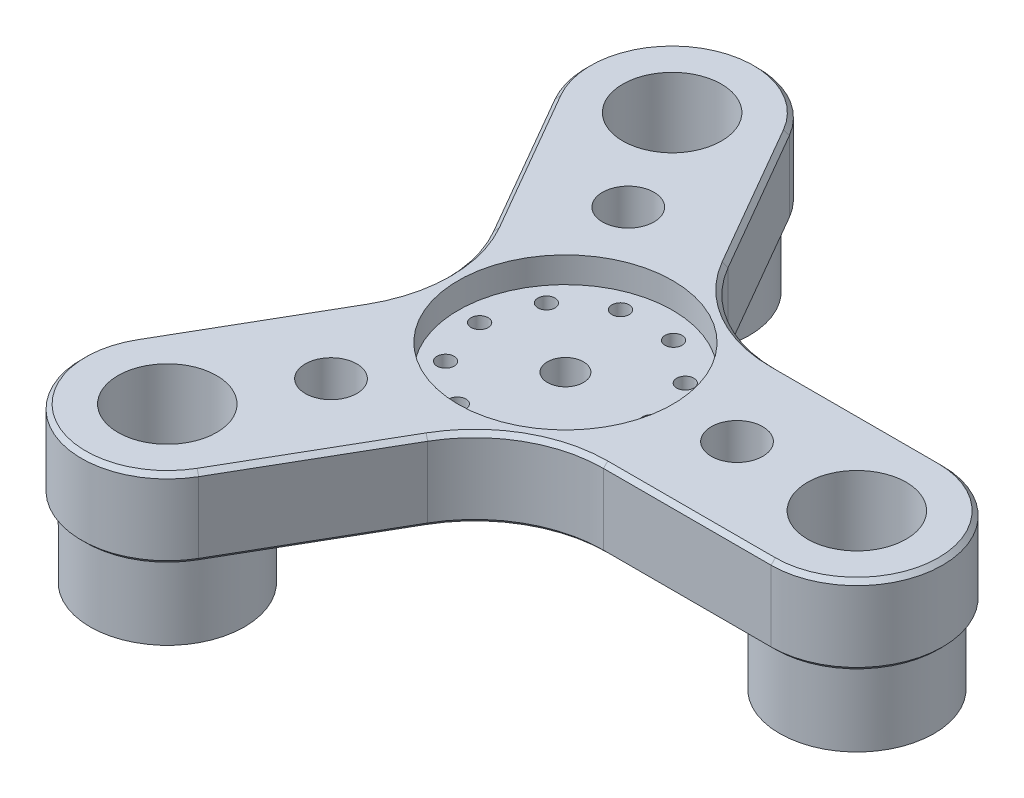
SolidWorks part; units mm, degrees
material "ﾒﾗﾐﾝ樹脂"
ref_plane "正面" through (0, 0, 0) normal (0, 0, 1) x (1, 0, 0)
ref_plane "平面" through (0, 0, 0) normal (0, 1, 0) x (1, 0, 0)
ref_plane "右側面" through (0, 0, 0) normal (1, 0, 0) x (0, 0, -1)
sketch "ｽｹｯﾁ1" plane through (0, 0, 0) normal (0, 1, 0) x (1, 0, 0)
  line L0 (-8.3244, -34.4182) -> (5.7735, -10)
  line L4 (-25.6449, -24.4182) -> (-11.547, 0)
  line L5 (-25.6449, 24.4182) -> (-11.547, 0)
  line L6 (-8.3244, 34.4182) -> (5.7735, 10)
  line L9 (33.9692, -10) -> (5.7735, -10)
  line L10 (33.9692, 10) -> (5.7735, 10)
  circle A1 centre (-16.9846, 29.4182) radius 5.75
  circle A2 centre (-16.9846, -29.4182) radius 5.75
  circle A3 centre (33.9692, 0) radius 5.75
  arc A4 (33.9692, -10) -> (33.9692, 10) centre (33.9692, 0) ccw
  arc A5 (-25.6449, -24.4182) -> (-8.3244, -34.4182) centre (-16.9846, -29.4182) ccw
  arc A6 (-8.3244, 34.4182) -> (-25.6449, 24.4182) centre (-16.9846, 29.4182) ccw
  point P26 (0, 0)
  point P39 (0, 0)
  dimension "D1" = 3
  dimension "D2" = 3
extrude "ﾎﾞｽ - 押し出し1" add sketch "ｽｹｯﾁ1" along normal blind 9.25
fillet "ﾌｨﾚｯﾄ1" radius 15 3 edges at (-11.547, 4.625, 0) (5.7735, 4.625, -10) (5.7735, 4.625, 10)
sketch "ｽｹｯﾁ2" plane through (0, 9.25, 0) normal (0, 1, 0) x (1, 0, 0)
  circle A0 centre (0, 0) radius 12.5
extrude "ｶｯﾄ - 押し出し1" cut sketch "ｽｹｯﾁ2" against normal blind 3
sketch "ｽｹｯﾁ3" plane through (0, 6.25, 0) normal (0, 1, 0) x (1, 0, 0)
  circle A0 centre (0, 0) radius 2.1
extrude "ｶｯﾄ - 押し出し2" cut sketch "ｽｹｯﾁ3" against normal through all
sketch "ｽｹｯﾁ4" plane through (0, 6.25, 0) normal (0, 1, 0) x (1, 0, 0)
  circle A0 centre (10, 0) radius 1
  circle A1 centre (8.0902, -5.8779) radius 1
  circle A2 centre (3.0902, -9.5106) radius 1
  circle A3 centre (-3.0902, -9.5106) radius 1
  circle A4 centre (-8.0902, -5.8779) radius 1
  circle A5 centre (-10, 0) radius 1
  circle A6 centre (-8.0902, 5.8779) radius 1
  circle A7 centre (-3.0902, 9.5106) radius 1
  circle A8 centre (3.0902, 9.5106) radius 1
  circle A9 centre (8.0902, 5.8779) radius 1
  point P24 (0, 0)
  dimension "D1" = 10
extrude "ｶｯﾄ - 押し出し3" cut sketch "ｽｹｯﾁ4" against normal through all
sketch "ｽｹｯﾁ5" plane through (0, 0, 0) normal (0, -1, 0) x (1, 0, 0)
  circle A0 centre (-16.9846, -29.4182) radius 9
  circle A1 centre (-16.9846, 29.4182) radius 9
  circle A2 centre (33.9692, 0) radius 9
  circle A3 centre (-16.9846, -29.4182) radius 5.75
  circle A4 centre (-16.9846, 29.4182) radius 5.75
  circle A5 centre (33.9692, 0) radius 5.75
  point P10 (0, 0)
  point P15 (0, 0)
  dimension "D1" = 3
  dimension "D2" = 3
extrude "ﾎﾞｽ - 押し出し2" add sketch "ｽｹｯﾁ5" along normal blind 8.75
sketch "ｽｹｯﾁ6" plane through (0, 0, 0) normal (0, -1, 0) x (1, 0, 0)
  circle A0 centre (0, 0) radius 4.71
  circle A1 centre (0, 0) radius 2.1
extrude "ﾎﾞｽ - 押し出し3" add sketch "ｽｹｯﾁ6" along normal blind 2.5
chamfer "面取り1" distance 0.5 angle 45 12 edges at (-3.4405, 0, -25.9591) (-21.9846, 0, -38.0785) (-20.761, 0, -15.9591) (-13.8675, 0, 0) (-20.761, 0, 15.9591) (-21.9846, 0, 38.0785) (-3.4405, 0, 25.9591) (6.9338, 0, 12.0096) (24.2015, 0, 10) (43.9692, 0, 0) (24.2015, 0, -10) (6.9338, 0, -12.0096)
chamfer "面取り2" distance 0.5 angle 45 12 edges at (6.9338, 9.25, -12.0096) (24.2015, 9.25, -10) (43.9692, 9.25, 0) (24.2015, 9.25, 10) (6.9338, 9.25, 12.0096) (-3.4405, 9.25, 25.9591) (-21.9846, 9.25, 38.0785) (-20.761, 9.25, 15.9591) (-13.8675, 9.25, 0) (-20.761, 9.25, -15.9591) (-21.9846, 9.25, -38.0785) (-3.4405, 9.25, -25.9591)
sketch "ｽｹｯﾁ7" plane through (0, 9.25, 0) normal (0, 1, 0) x (1, 0, 0)
  circle A0 centre (20, 0) radius 3
  circle A1 centre (-10, -17.3205) radius 3
  circle A2 centre (-10, 17.3205) radius 3
  point P9 (0, 0)
  dimension "D1" = 3
extrude "ｶｯﾄ - 押し出し4" cut sketch "ｽｹｯﾁ7" against normal through all
